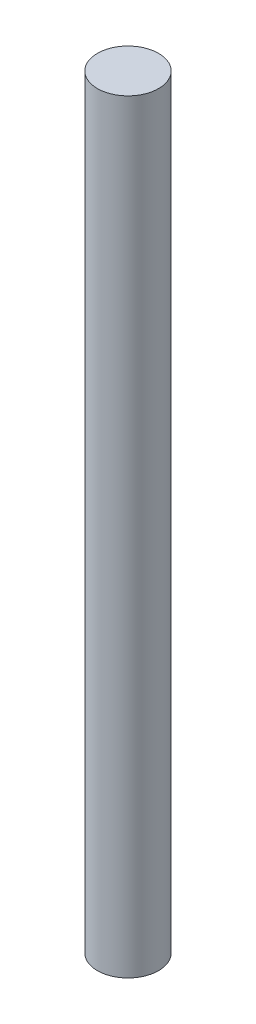
SolidWorks part; units mm, degrees
material "1060 Alloy"
ref_plane "Front Plane" through (0, 0, 0) normal (0, 0, 1) x (1, 0, 0)
ref_plane "Top Plane" through (0, 0, 0) normal (0, 1, 0) x (1, 0, 0)
ref_plane "Right Plane" through (0, 0, 0) normal (1, 0, 0) x (0, 0, -1)
sketch "Sketch1" plane through (0, 0, 0) normal (0, 1, 0) x (1, 0, 0)
  circle A0 centre (0, 0) radius 2
  dimension "D1" = 4
extrude "Boss-Extrude1" add sketch "Sketch1" along normal blind 50
